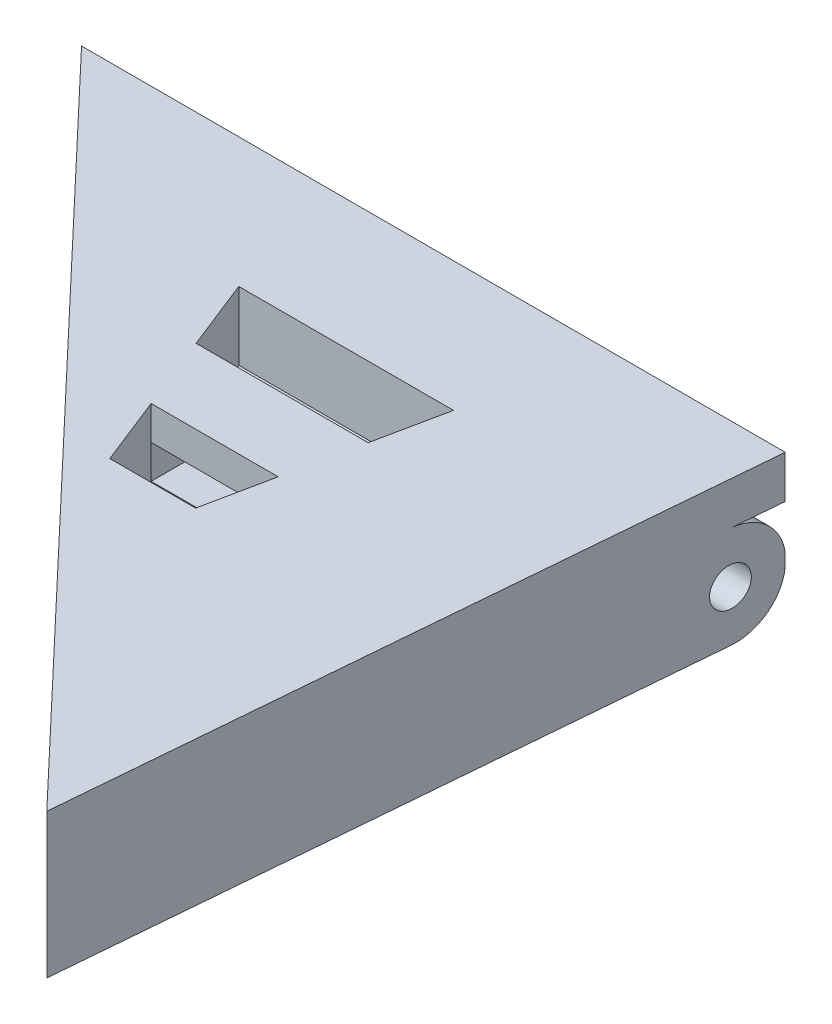
SolidWorks part; units mm, degrees
ref_plane "Front Plane" through (0, 0, 0) normal (0, 0, 1) x (1, 0, 0)
ref_plane "Top Plane" through (0, 0, 0) normal (0, 1, 0) x (1, 0, 0)
ref_plane "Right Plane" through (0, 0, 0) normal (1, 0, 0) x (0, 0, -1)
sketch "Sketch1" plane through (0, 0, 0) normal (0, 1, 0) x (1, 0, 0)
  line L0 (0, 0) -> (21.1386, 0)
  line L1 (21.1386, 0) -> (21.1386, 6.0053)
  line L2 (21.1386, 6.0053) -> (28.9856, 6.0053)
  line L3 (28.9856, 6.0053) -> (25.5142, -34.4862)
  line L4 (0, 0) -> (0, 6.0053)
  line L5 (0, 6.0053) -> (-12.9078, 6.0053)
  line L6 (-12.9078, 6.0053) -> (25.5142, -34.4862)
  dimension "D1" = 85.1
extrude "Boss-Extrude1" add sketch "Sketch1" along normal blind 15.24
sketch "Sketch2" plane through (0, 15.24, 0) normal (0, 1, 0) x (1, 0, 0)
  line L0 (21.1386, 0) -> (28.4707, 0)
  line L1 (25.5142, -34.4862) -> (28.9856, 6.0053) construction
  line L2 (28.4707, 0) -> (28.9856, 6.0053)
  line L3 (28.9856, 6.0053) -> (21.1386, 6.0053)
  line L4 (21.1386, 6.0053) -> (21.1386, 0)
  line L5 (0, 0) -> (-7.2095, 0)
  line L6 (-12.9078, 6.0053) -> (25.5142, -34.4862) construction
  line L7 (-7.2095, 0) -> (-12.9078, 6.0053)
  line L8 (-12.9078, 6.0053) -> (0, 6.0053)
  line L9 (0, 6.0053) -> (0, 0)
extrude "Cut-Extrude1" cut sketch "Sketch2" against normal blind 2.54
sketch "Sketch3" plane through (0, 0, 0) normal (1, 0, 0) x (0, 0, -1)
  line L0 (6.0053, 12.7) -> (6.0053, 0) construction
  line L1 (0, 12.7) -> (6.0053, 12.7)
  line L2 (0, 12.7) -> (0, 6.645)
  line L3 (0, 6.645) -> (6.0053, 6.645)
  line L4 (6.0053, 12.7) -> (6.0053, 6.645)
  line L5 (6.0053, 6.645) -> (0, 12.7)
  line L6 (0, 6.645) -> (0, 0)
  line L7 (0, 0) -> (6.0053, 0)
  line L8 (-34.4862, 0) -> (6.0053, 0) construction
  line L9 (6.0053, 0) -> (6.0053, 6.645)
  line L10 (0, 6.645) -> (-34.4862, 6.645)
  line L11 (-34.4862, 15.24) -> (-34.4862, 0) construction
  line L12 (-34.4862, 6.645) -> (-34.4862, 0)
  line L13 (-34.4862, 0) -> (0, 0)
  circle A0 centre (3.0026, 9.6725) radius 3.0275
  circle A1 centre (3.0026, 9.6725) radius 1.1451
  line M1 (6.0053, 0) -> (6.0053, 12.7)
  line M2 (6.0053, 12.7) -> (0, 12.7)
  line M3 (0, 12.7) -> (0, 0)
  line M4 (0, 0) -> (6.0053, 0)
extrude "Cut-Extrude2" cut sketch "Sketch3" against normal blind 19.812 and the other way blind 34.544 contours A0 M1 M2 | L5 A1 | L5 A1 | A0 L3 L5 | A0 L5 M1 | L3 M3 M4 M1 | L12 L13 L10 M3
sketch "Sketch4" plane through (0, 15.24, 0) normal (0, 1, 0) x (1, 0, 0)
  line L0 (0, 0) -> (21.1386, 0)
  line L1 (10.5693, 0) -> (10.5693, -25.8703) construction
  line L2 (10.5693, -1.7096) -> (10.5693, -14.424)
  line L3 (10.5693, -14.424) -> (14.3126, -14.424)
  line L4 (10.5693, -1.7096) -> (16.949, -1.7096)
  line L5 (16.949, -1.7096) -> (14.3126, -14.424)
  line L6 (10.5693, -14.424) -> (9.2069, -14.424)
  line L7 (10.5693, -1.7096) -> (4.1678, -1.7096)
  line L8 (4.1678, -1.7096) -> (9.2069, -14.424)
  line L9 (10.5693, -1.7096) -> (10.5693, -5.9143)
  line L10 (10.5693, -5.9143) -> (16.0771, -5.9143)
  line L11 (10.5693, -5.9143) -> (5.8343, -5.9143)
  line L12 (10.5693, -5.9143) -> (10.5693, -10.3527)
  line L13 (10.5693, -10.3527) -> (15.1568, -10.3527)
  line L14 (15.1568, -10.3527) -> (7.5933, -10.3527)
extrude "Cut-Extrude3" cut sketch "Sketch4" against normal blind 4.064 contours L11 L2 L7 L8 | L2 L10 L5 L4 | L2 L14 L8 L6 | L13 L2 L3 L5
sketch "Sketch5" plane through (0, 0, 10.3527) normal (0, 0, 1) x (1, 0, 0)
  line L1 (7.5933, 15.24) -> (15.2424, 15.24)
  line L2 (7.5933, 15.24) -> (7.5933, 11.2251)
  line L3 (7.5933, 11.2251) -> (15.2424, 11.2251)
  line L4 (15.2424, 15.24) -> (15.2424, 11.2251)
  line L5 (15.2424, 11.2251) -> (7.5933, 11.2251)
  line L6 (15.2424, 11.2251) -> (15.2424, 13.2325)
  line L7 (15.2424, 13.2325) -> (7.5933, 13.2325)
  line L8 (7.5933, 11.2251) -> (7.5933, 13.2325)
  line M4 (15.1568, 11.176) -> (15.1568, 15.24)
extrude "Cut-Extrude4" cut sketch "Sketch5" against normal blind 6.604 contours L7 L2 L3 M4
sketch "Sketch6" plane through (0, 15.24, 0) normal (0, 1, 0) x (1, 0, 0)
  line L0 (28.4707, 0) -> (28.9856, 6.0053)
  line L1 (28.9856, 6.0053) -> (-12.9078, 6.0053)
  line L2 (-12.9078, 6.0053) -> (-7.2095, 0)
  line L3 (-7.2095, 0) -> (28.4707, 0)
extrude "Boss-Extrude2" add sketch "Sketch6" against normal blind 2.54
